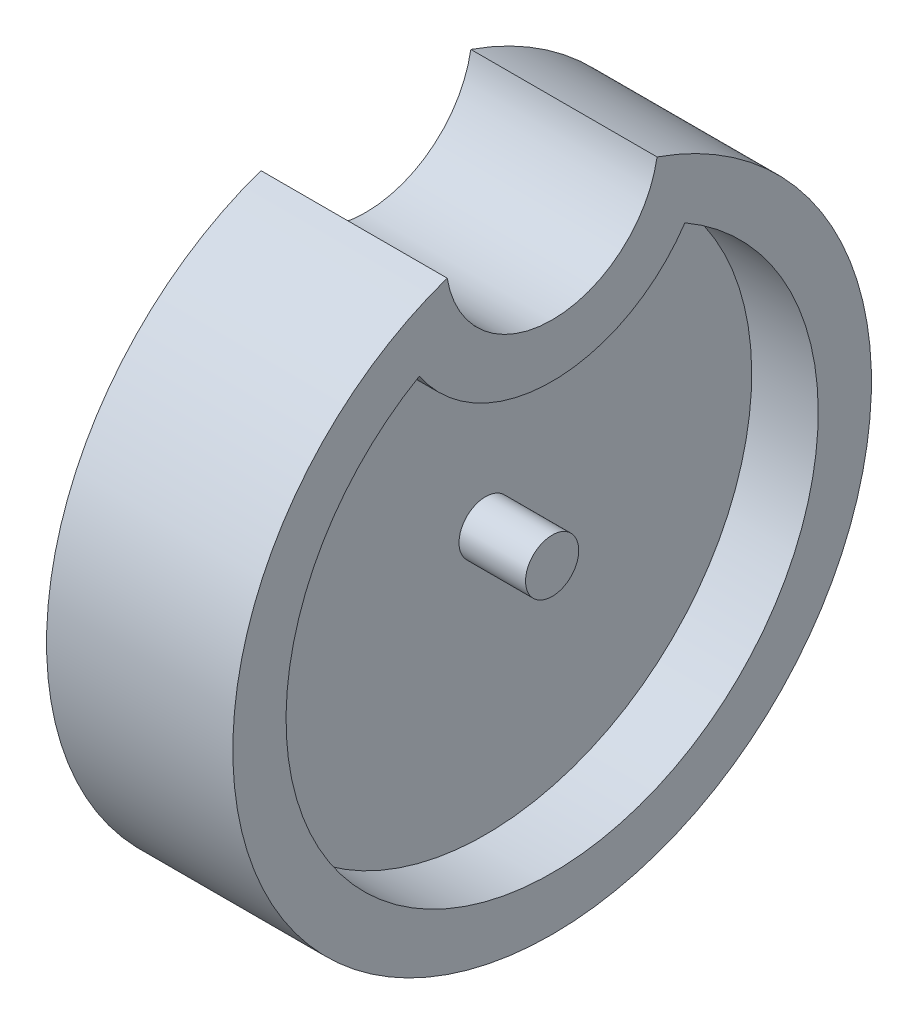
SolidWorks part; units mm, degrees
material "PE High Density"
ref_plane "Front Plane" through (0, 0, 0) normal (0, 0, 1) x (1, 0, 0)
ref_plane "Top Plane" through (0, 0, 0) normal (0, 1, 0) x (1, 0, 0)
ref_plane "Right Plane" through (0, 0, 0) normal (1, 0, 0) x (0, 0, -1)
sketch "Sketch1" plane through (0, 0, 0) normal (1, 0, 0) x (0, 0, -1)
  arc A0 (-6.2612, 17.9917) -> (6.2612, 17.9917) centre (0, 0) ccw
  arc A1 (-6.2612, 17.9917) -> (6.2612, 17.9917) centre (0, 19.05) ccw
  arc A2 (-7.9198, 13.7583) -> (7.9198, 13.7583) centre (0, 19.05) ccw
  arc A3 (-7.9198, 13.7583) -> (7.9198, 13.7583) centre (0, 0) ccw
  point P4 (0, 0)
  point P5 (0, 9.525)
  point P8 (0, 12.7)
  dimension "D1" = 3.175
  dimension "D2" = 3.175
  dimension "D3" = 38.1
  dimension "D4" = 6.35
extrude "Boss-Extrude1" add sketch "Sketch1" along normal mid plane 11.1125
sketch "Sketch3" plane through (0, 0, 0) normal (1, 0, 0) x (0, 0, -1)
  arc A0 (-7.9198, 13.7583) -> (7.9198, 13.7583) centre (0, 0) ccw
  arc A1 (-7.9198, 13.7583) -> (7.9198, 13.7583) centre (0, 19.05) ccw
  arc A2 (-7.9198, 13.7583) -> (7.9198, 13.7583) centre (0, 0) ccw construction
  arc A3 (-7.9198, 13.7583) -> (7.9198, 13.7583) centre (0, 19.05) ccw construction
extrude "Boss-Extrude2" add sketch "Sketch3" along normal mid plane 3.175 contours A1 A0
sketch "Sketch6" plane through (0, 0, 0) normal (1, 0, 0) x (0, 0, -1)
  circle A0 centre (0, 0) radius 1.5875
  dimension "D1" = 3.175
extrude "Boss-Extrude3" add sketch "Sketch6" along normal mid plane 11.1125
